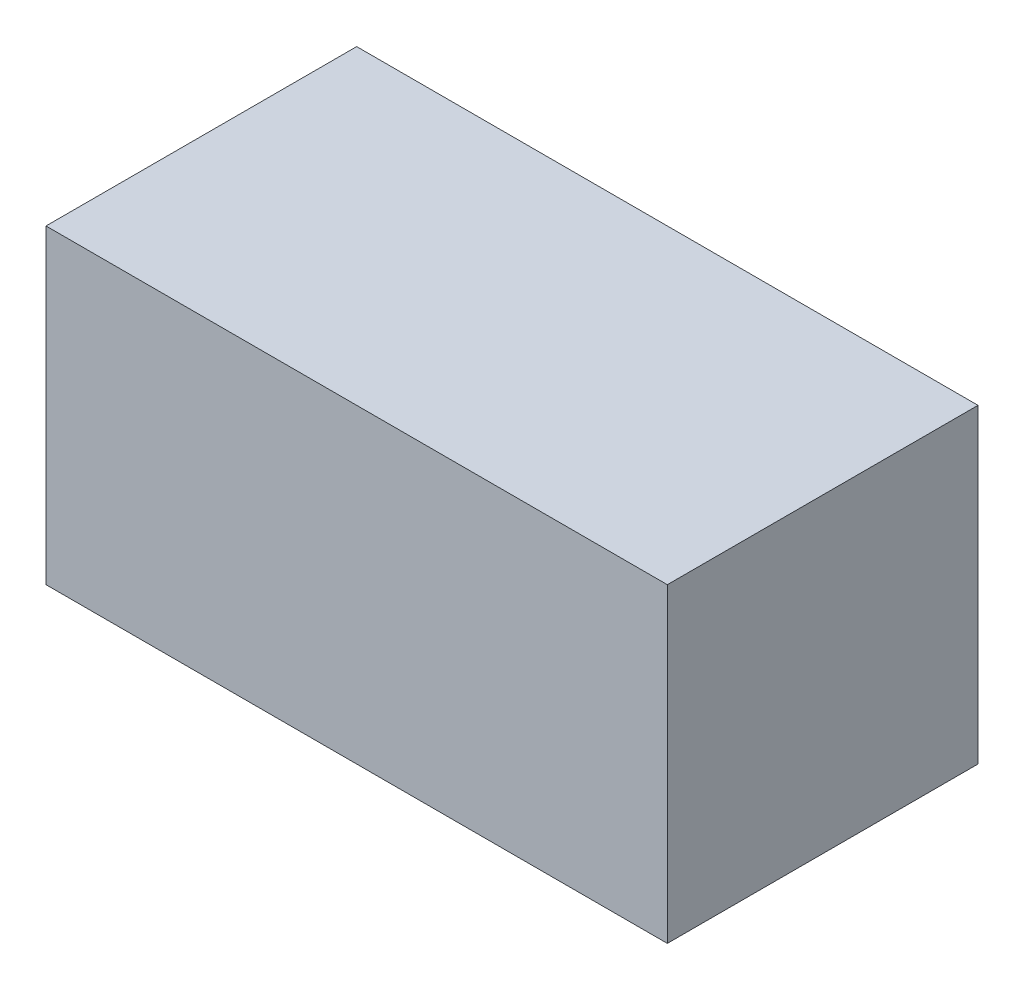
SolidWorks part; units mm, degrees
ref_plane "Front Plane" through (0, 0, 0) normal (0, 0, 1) x (1, 0, 0)
ref_plane "Top Plane" through (0, 0, 0) normal (0, 1, 0) x (1, 0, 0)
ref_plane "Right Plane" through (0, 0, 0) normal (1, 0, 0) x (0, 0, -1)
sketch "Sketch1" plane through (0, 0, 0) normal (0, 1, 0) x (1, 0, 0)
  line L1 (-50, 25) -> (50, 25)
  line L2 (-50, 25) -> (-50, -25)
  line L3 (-50, -25) -> (50, -25)
  line L4 (50, 25) -> (50, -25)
  line L5 (-50, 25) -> (50, -25) construction
  line L6 (-50, -25) -> (50, 25) construction
  point P0 (0, 0)
  dimension "D1" = 100
  dimension "D2" = 50
extrude "Boss-Extrude1" add sketch "Sketch1" along normal blind 50
